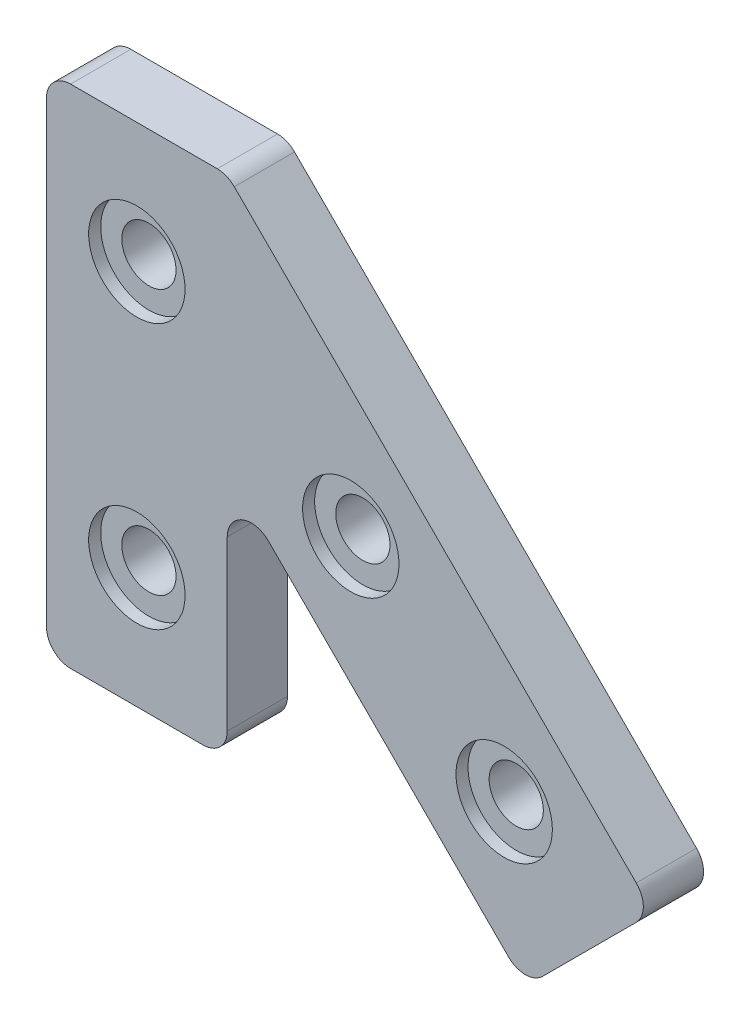
SolidWorks part; units mm, degrees
ref_plane "Front Plane" through (0, 0, 0) normal (0, 0, 1) x (1, 0, 0)
ref_plane "Top Plane" through (0, 0, 0) normal (0, 1, 0) x (1, 0, 0)
ref_plane "Right Plane" through (0, 0, 0) normal (1, 0, 0) x (0, 0, -1)
sketch "Sketch1" plane through (0, 0, 0) normal (0, 0, 1) x (1, 0, 0)
  line L0 (0, 0) -> (0, 42)
  line L1 (0, 42) -> (15, 42)
  line L2 (15, 42) -> (50.3553, 6.6447)
  line L3 (50.3553, 6.6447) -> (39.7487, -3.9619)
  line L4 (0, 0) -> (15, 0)
  line L5 (15, 0) -> (15, 20.7868)
  line L6 (39.7487, -3.9619) -> (15, 20.7868)
  point P8 (15, 13.6521)
  dimension "D1" = 15
  dimension "D2" = 42
  dimension "D3" = 15
  dimension "D4" = 135
  dimension "D5" = 15
  dimension "D6" = 50
extrude "Boss-Extrude1" add sketch "Sketch1" along normal blind 5
sketch "Sketch2" plane through (0, 0, 5) normal (0, 0, 1) x (1, 0, 0)
  line L0 (0, 0) -> (15, 0) construction
  line L1 (39.7487, -3.9619) -> (50.3553, 6.6447) construction
  circle A0 centre (7.5, 10) radius 4
  circle A1 centre (7.5, 32) radius 4
  circle A2 centre (37.981, 8.4124) radius 4
  circle A3 centre (25.253, 21.1403) radius 4
  dimension "D1" = 10
  dimension "D2" = 22
  dimension "D3" = 10
  dimension "D4" = 18
extrude "Cut-Extrude1" cut sketch "Sketch2" against normal blind 1
sketch "Sketch3" plane through (0, 0, 4) normal (0, 0, 1) x (1, 0, 0)
  circle A0 centre (7.5, 32) radius 2.25
  circle A1 centre (7.5, 10) radius 2.25
  circle A2 centre (25.253, 21.1403) radius 2.25
  circle A3 centre (37.981, 8.4124) radius 2.25
extrude "Cut-Extrude2" cut sketch "Sketch3" against normal blind 16
fillet "Fillet1" radius 2 7 edges at (15, 42, 2.5) (0, 42, 2.5) (15, 20.7868, 2.5) (50.3553, 6.6447, 2.5) (39.7487, -3.9619, 2.5) (15, 0, 2.5) (0, 0, 2.5)
